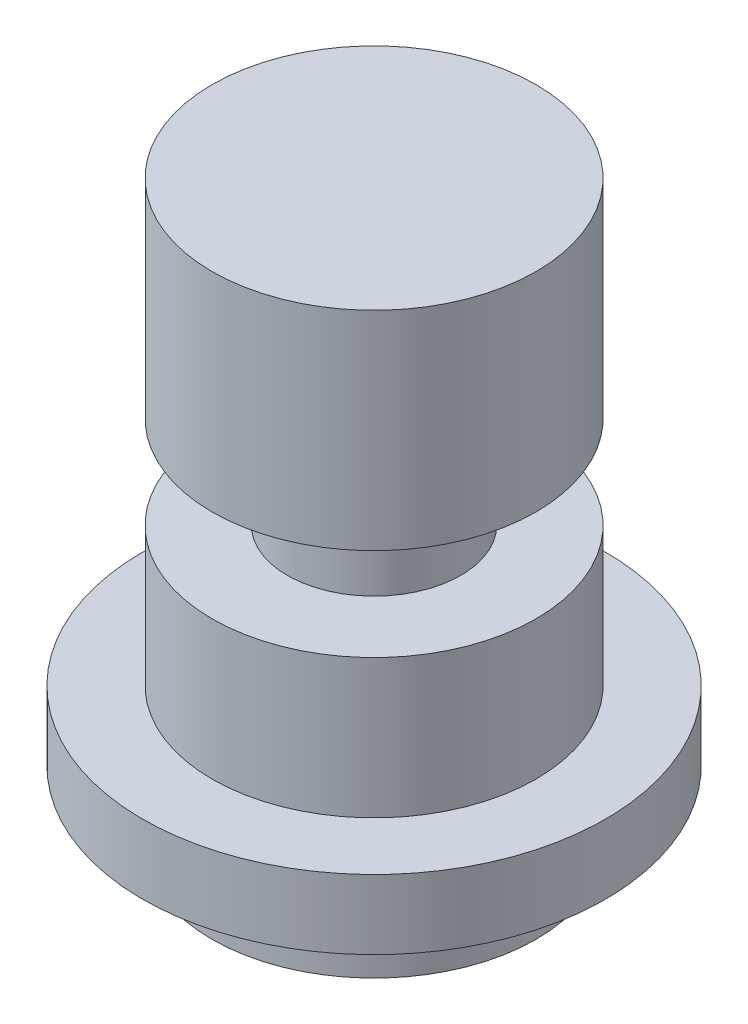
SolidWorks part; units mm, degrees
ref_plane "Front Plane" through (0, 0, 0) normal (0, 0, 1) x (1, 0, 0)
ref_plane "Top Plane" through (0, 0, 0) normal (0, 1, 0) x (1, 0, 0)
ref_plane "Right Plane" through (0, 0, 0) normal (1, 0, 0) x (0, 0, -1)
sketch "Sketch1" plane through (0, 0, 0) normal (0, 0, 1) x (1, 0, 0)
  line L0 (0, 0) -> (-7, 0)
  line L1 (-7, 0) -> (-7, 3)
  line L2 (-7, 3) -> (-10, 3)
  line L3 (-10, 3) -> (-10, 6)
  line L4 (-10, 6) -> (-7, 6)
  line L5 (-7, 6) -> (-7, 12)
  line L6 (-7, 12) -> (-3.75, 12)
  line L7 (-3.75, 12) -> (-3.75, 16)
  line L8 (-3.75, 16) -> (-7, 16)
  line L9 (-7, 16) -> (-7, 25)
  line L10 (-7, 25) -> (0, 25)
  line L11 (0, 25) -> (0, 0)
  dimension "D1" = 7
  dimension "D2" = 7
  dimension "D3" = 25
  dimension "D4" = 10
  dimension "D5" = 7
  dimension "D6" = 9
  dimension "D7" = 10
  dimension "D8" = 4
  dimension "D9" = 3
revolve "Revolve1" add sketch "Sketch1" angle 360 about L11
